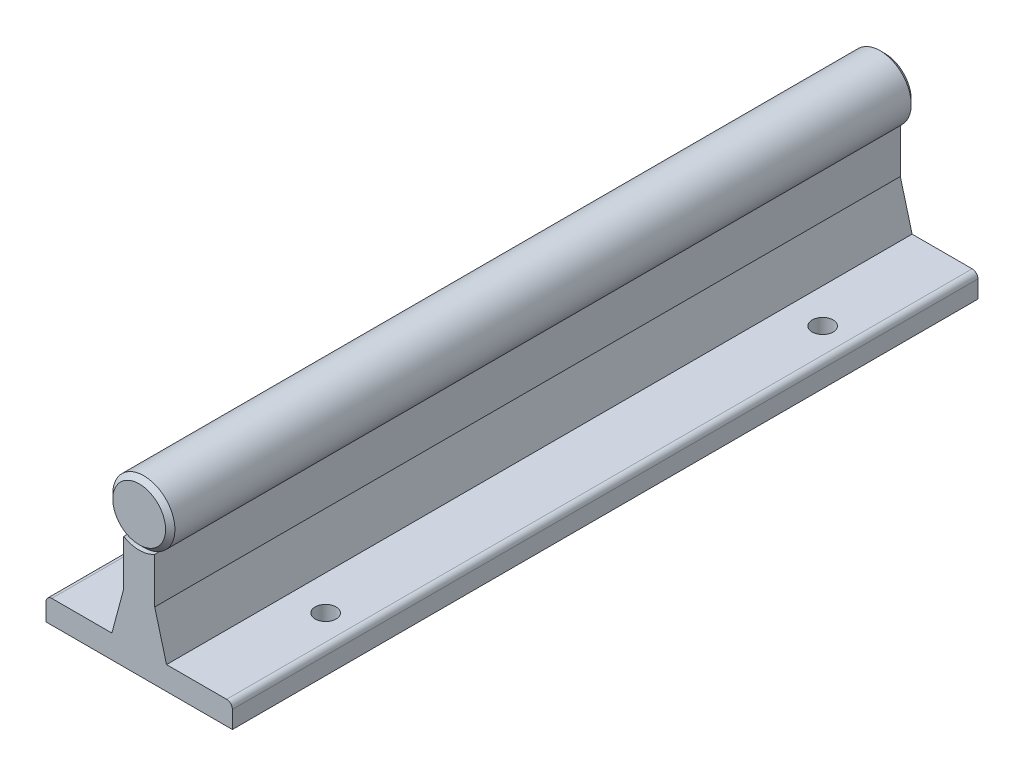
SolidWorks part; units mm, degrees
material "Ceramic Porcelain"
ref_plane "Front" through (0, 0, 0) normal (0, 0, 1) x (1, 0, 0)
ref_plane "Top" through (0, 0, 0) normal (0, 1, 0) x (1, 0, 0)
ref_plane "Right" through (0, 0, 0) normal (1, 0, 0) x (0, 0, -1)
sketch "Sketch1" plane through (0, 0, 0) normal (0, 0, 1) x (1, 0, 0)
  line L0 (-19.05, 0) -> (19.05, 0)
  line L1 (19.05, 0) -> (19.05, 4.7625)
  line L2 (19.05, 4.7625) -> (5.586, 4.7625)
  line L3 (-19.05, 4.7625) -> (-19.05, 0)
  line L4 (-3.175, 23.0757) -> (-3.175, 13.7604)
  line L5 (-3.175, 13.7604) -> (-5.586, 4.7625)
  line L6 (3.175, 23.0757) -> (3.175, 13.7604)
  line L7 (3.175, 13.7604) -> (5.586, 4.7625)
  line L8 (-5.586, 4.7625) -> (-19.05, 4.7625)
  arc A0 (3.175, 23.0757) -> (-3.175, 23.0757) centre (0, 28.575) ccw
  point P6 (-6.35, 28.575)
  dimension "D2" = 6.35
  dimension "shaft diam" = 12.7
  dimension "H" = 4.7625
  dimension "D" = 38.1
  dimension "A" = 28.575
  dimension "D6" = 15
extrude "Extrude1" add sketch "Sketch1" along normal mid plane 152.4
sketch "Sketch3" plane through (0, 0, 0) normal (1, 0, 0) x (0, 0, -1)
  line L0 (-76.2, 33.9725) -> (-75.2475, 34.925)
  line L3 (-76.2, 34.925) -> (-76.2, 23.0757) construction
  line L13 (-76.2, 34.925) -> (-76.2, 33.9725)
  line L14 (-76.2, 34.925) -> (-75.2475, 34.925)
  line L15 (76.2, 34.925) -> (-76.2, 34.925) construction
  dimension "D1" = 45
  dimension "D2" = 0.9525
revolve "Cut-Revolve1" cut sketch "Sketch3" angle 360 about axis through (0, 28.575, 76.2) along (0, 0, -1)
mirror "Mirror1" about plane through (0, 0, 0) normal (0, 0, 1) of "Cut-Revolve1"
fillet "Fillet1" radius 1.1906 2 edges at (19.05, 4.7625, 0) (-19.05, 4.7625, 0)
sketch "Sketch4" plane through (0, 0, 0) normal (0, 1, 0) x (1, 0, 0)
  line L0 (-19.05, -76.2) -> (19.05, -76.2) construction
  line L1 (-12.7, -50.8) -> (12.7, -50.8) construction
  circle A0 centre (12.7, -50.8) radius 2.1463
  circle A1 centre (-12.7, -50.8) radius 2.1463
  point P6 (0, -50.8)
  dimension "G" = 4.2926
  dimension "E" = 25.4
  dimension "C" = 25.4
extrude "Extrude3" cut sketch "Sketch4" along normal up to surface (4.7625 mm away) up to face at (-11.7227, 4.7625, 0)
pattern_linear "LPattern1" count 19 spacing 101.6 along (0, 0, -1) of "Extrude3"
sketch "Sketch6" plane through (0, 0, 0) normal (0, 0, 1) x (1, 0, 0)
  line L0 (-10.5537, 0) -> (-10.5537, 4.7625) construction
  line L1 (-14.8463, 4.7625) -> (-14.8463, 0) construction
  line L2 (10.5537, 4.7625) -> (10.5537, 0) construction
  line L3 (14.8463, 0) -> (14.8463, 4.7625) construction
  line L4 (-10.5537, 0) -> (-10.5537, 4.7625)
  line L5 (-14.8463, 4.7625) -> (-14.8463, 0)
  line L6 (10.5537, 4.7625) -> (10.5537, 0)
  line L7 (14.8463, 0) -> (14.8463, 4.7625)
sketch "Sketch7" plane through (0, 0, 0) normal (1, 0, 0) x (0, 0, -1)
  line L4 (48.6537, 4.7625) -> (48.6537, 0) construction
  line L5 (52.9463, 0) -> (52.9463, 4.7625) construction
  line L6 (52.9463, 0) -> (52.9463, 4.7625) construction
  line L7 (48.6537, 4.7625) -> (48.6537, 0) construction
  line L8 (-52.9463, 4.7625) -> (-52.9463, 0) construction
  line L9 (-48.6537, 0) -> (-48.6537, 4.7625) construction
  line L10 (-48.6537, 0) -> (-48.6537, 4.7625) construction
  line L11 (-52.9463, 4.7625) -> (-52.9463, 0) construction
  line L12 (48.6537, 4.7625) -> (48.6537, 0)
  line L13 (52.9463, 0) -> (52.9463, 4.7625)
  line L14 (52.9463, 0) -> (52.9463, 4.7625)
  line L15 (48.6537, 4.7625) -> (48.6537, 0)
  line L16 (48.6537, 4.7625) -> (48.6537, 0)
  line L17 (52.9463, 0) -> (52.9463, 4.7625)
  line L18 (52.9463, 0) -> (52.9463, 4.7625)
  line L19 (48.6537, 4.7625) -> (48.6537, 0)
  line L20 (-52.9463, 4.7625) -> (-52.9463, 0)
  line L21 (-48.6537, 0) -> (-48.6537, 4.7625)
  line L22 (-48.6537, 0) -> (-48.6537, 4.7625)
  line L23 (-52.9463, 4.7625) -> (-52.9463, 0)
  line L24 (-52.9463, 4.7625) -> (-48.6537, 4.7625) construction
  line L26 (-52.9463, 4.7625) -> (-76.2, 4.7625) construction
  line L27 (-76.2, 0) -> (-76.2, 3.5719) construction
  line L28 (48.6537, 4.7625) -> (52.9463, 4.7625) construction
  line L29 (52.9463, 4.7625) -> (76.2, 4.7625) construction
  line L30 (76.2, 0) -> (76.2, 3.5719) construction
  line L31 (-76.2, 4.7625) -> (76.2, 4.7625) construction
  line L32 (-76.2, 0) -> (76.2, 0) construction
sketch "Sketch8" plane through (0, 4.7625, 0) normal (0, 1, 0) x (1, 0, 0)
  circle A1 centre (12.7, -50.8) radius 2.1463 construction
  circle A2 centre (12.7, -50.8) radius 2.1463
equation "\"D2@Sketch3\" = \"shaft diam@Sketch1\" * .075"
equation "\"D1@Fillet1\" = \"H@Sketch1\" * .25"
